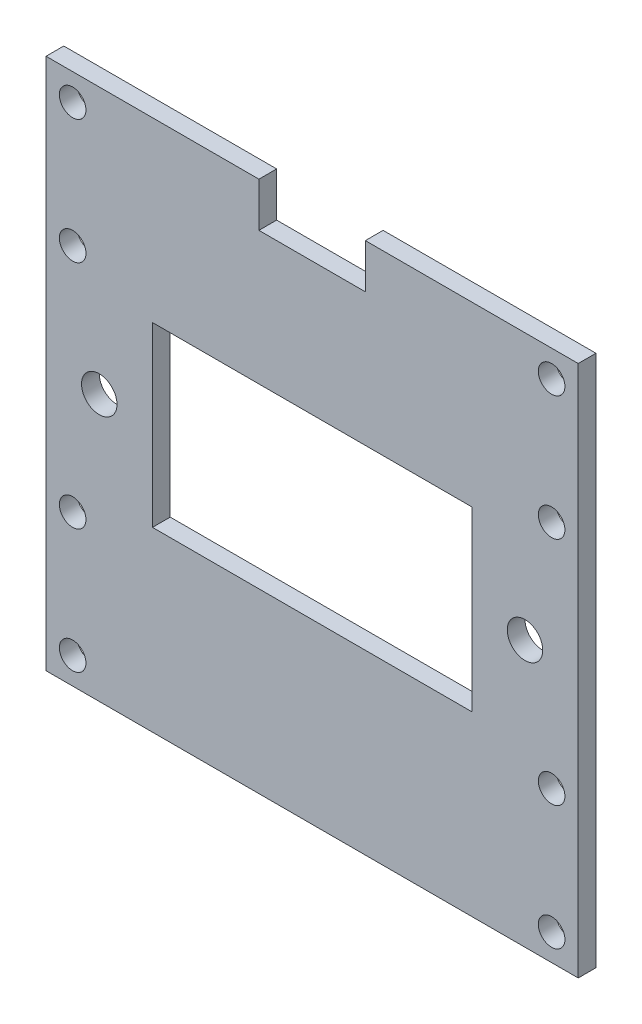
SolidWorks part; units mm, degrees
material "1060 Alloy"
ref_plane "Front Plane" through (0, 0, 0) normal (0, 0, 1) x (1, 0, 0)
ref_plane "Top Plane" through (0, 0, 0) normal (0, 1, 0) x (1, 0, 0)
ref_plane "Right Plane" through (0, 0, 0) normal (1, 0, 0) x (0, 0, -1)
sketch "Sketch1" plane through (0, 0, 0) normal (0, 0, 1) x (1, 0, 0)
  line L0 (36, 0) -> (60, 0)
  line L1 (0, 0) -> (24, 0)
  line L2 (0, 0) -> (0, 60)
  line L3 (0, 60) -> (24, 60)
  line L4 (60, 0) -> (60, 60)
  line L5 (12, 40) -> (48, 40)
  line L6 (12, 40) -> (12, 20)
  line L7 (12, 20) -> (48, 20)
  line L8 (48, 40) -> (48, 20)
  line L9 (36, 60) -> (60, 60)
  line L13 (24, 0) -> (36, 0)
  line L14 (24, 60) -> (24, 55)
  line L15 (24, 55) -> (36, 55)
  line L16 (36, 60) -> (36, 55)
  circle A0 centre (3, 57) radius 1.5
  circle A1 centre (3, 43) radius 1.5
  circle A2 centre (57, 57) radius 1.5
  circle A3 centre (57, 43) radius 1.5
  circle A4 centre (57, 17) radius 1.5
  circle A5 centre (57, 3) radius 1.5
  circle A6 centre (3, 17) radius 1.5
  circle A7 centre (3, 3) radius 1.5
  circle A8 centre (6, 30) radius 2
  circle A9 centre (54, 30) radius 2
  dimension "D1" = 3
  dimension "D15" = 4
  dimension "D2" = 3
  dimension "D3" = 3
  dimension "D4" = 3
  dimension "D5" = 3
  dimension "D6" = 14
  dimension "D7" = 14
  dimension "D8" = 60
  dimension "D9" = 60
  dimension "D10" = 30
  dimension "D11" = 20
  dimension "D12" = 20
  dimension "D13" = 12
  dimension "D14" = 12
  dimension "D16" = 6
  dimension "D17" = 6
  dimension "D20" = 5
  dimension "D21" = 24
extrude "Boss-Extrude1" add sketch "Sketch1" along normal blind 2
